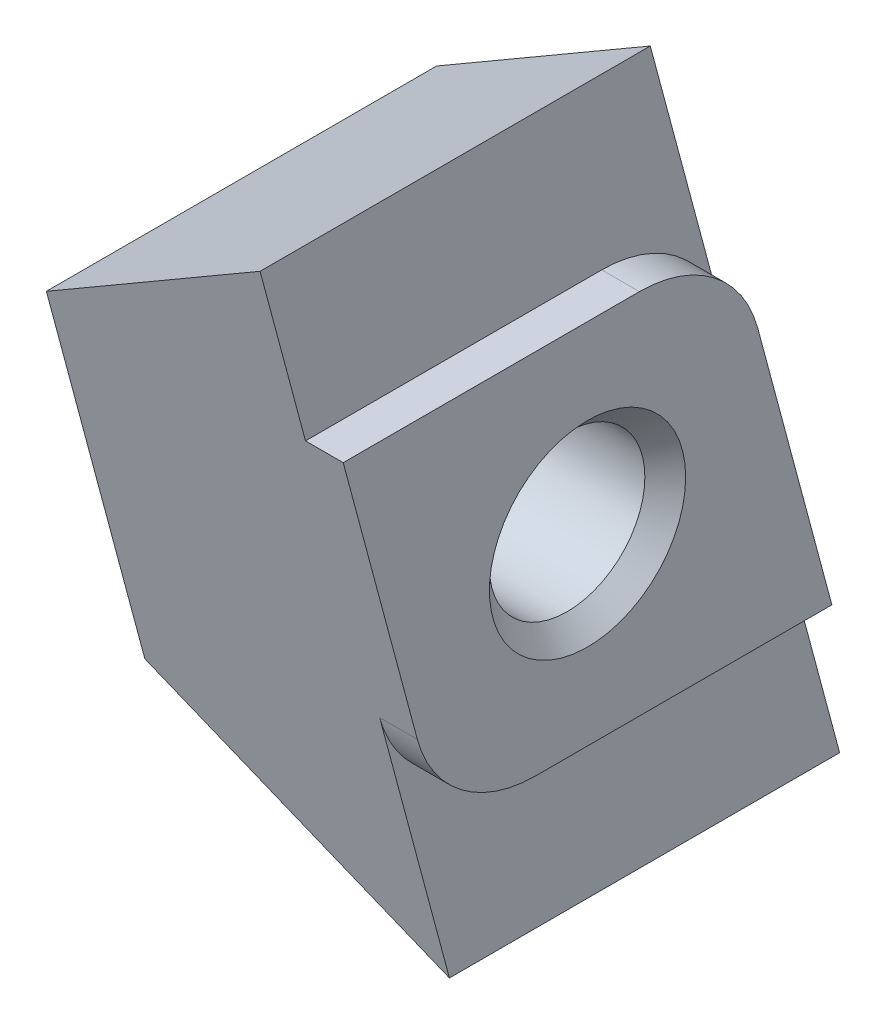
SolidWorks part; units mm, degrees
ref_plane "Piano frontale" through (0, 0, 0) normal (0, 0, 1) x (1, 0, 0)
ref_plane "Piano superiore" through (0, 0, 0) normal (0, 1, 0) x (1, 0, 0)
ref_plane "Piano destro" through (0, 0, 0) normal (1, 0, 0) x (0, 0, -1)
sketch "Sketch1" plane through (0, 0, 0) normal (1, 0, 0) x (0, 0, -1)
  line L0 (1.1011, 3.9) -> (-5.1861, 3.9)
  line L1 (-5.1861, 3.9) -> (-3.6125, -1.9729)
  line L2 (-1.1011, -3.9) -> (5.1861, -3.9)
  line L3 (5.1861, -3.9) -> (3.6125, 1.9729)
  arc A0 (-3.6125, -1.9729) -> (-1.1011, -3.9) centre (-1.1011, -1.3) ccw
  arc A1 (3.6125, 1.9729) -> (1.1011, 3.9) centre (1.1011, 1.3) ccw
extrude "Extrude1" add sketch "Sketch1" against normal blind 0.8
sketch "Sketch2" plane through (-0.8, 0, 0) normal (-1, 0, 0) x (0, 0, 1)
  line L0 (2.1315, -7.5) -> (-6.1507, -7.5)
  line L1 (-2.1315, 7.5) -> (6.1507, 7.5)
  spline S0 degree 3 poles (-2.1315, 7.5) (-3.4712, 2.5) (-4.811, -2.5) (-6.1507, -7.5) knots 0 0 0 0 1 1 1 1
  spline S1 degree 3 poles (2.1315, -7.5) (3.4712, -2.5) (4.811, 2.5) (6.1507, 7.5) knots 0 0 0 0 1 1 1 1
extrude "Extrude2" add sketch "Sketch2" along normal blind 5.5
draft "Draft1" type of draft neutral plane draft angle 33.207 faces to draft 1 face at (-3.55, 7.5, 2.0096) neutral plane through (-0.8, 0, 4.1411) neutral plane normal (1, 0, 0) reverse direction yes parameters "D1"=33.207
draft "Draft2" type of draft neutral plane draft angle 33.207 faces to draft 1 face at (-3.55, -7.5, -2.0096) neutral plane through (-0.8, 0, 4.1411) neutral plane normal (1, 0, 0) reverse direction yes parameters "D1"=33.207
hole_wizard "M4 Tapped Hole1" positions "Sketch4" profile "Sketch3" tap size "M4" standard "ISO" end condition up to next
sketch "Sketch4" plane through (-6.3, 0, 0) normal (-1, 0, 0) x (0, 0, 1)
  point P0 (0, 0)
sketch "Sketch3" plane through (-6.3, 0, 0) normal (0, 1, 0) x (0, 0, 1)
  line L0 (0, 0) -> (0, 6.3)
  line L1 (0, 6.3) -> (1.65, 6.3)
  line L2 (1.65, 6.3) -> (1.65, 0)
  line L5 (1.65, 0) -> (0, 0)
  line L11 (0, -6.35) -> (0, 107.95) construction
  dimension "Thread Major Dia." = 3.3
  dimension "Thru Tap Drill Depth" = 6.3
chamfer "Chamfer1" distance 0.433 angle 45 2 edges at (0, 0, -1.65) (-6.3, 0, 1.65)
